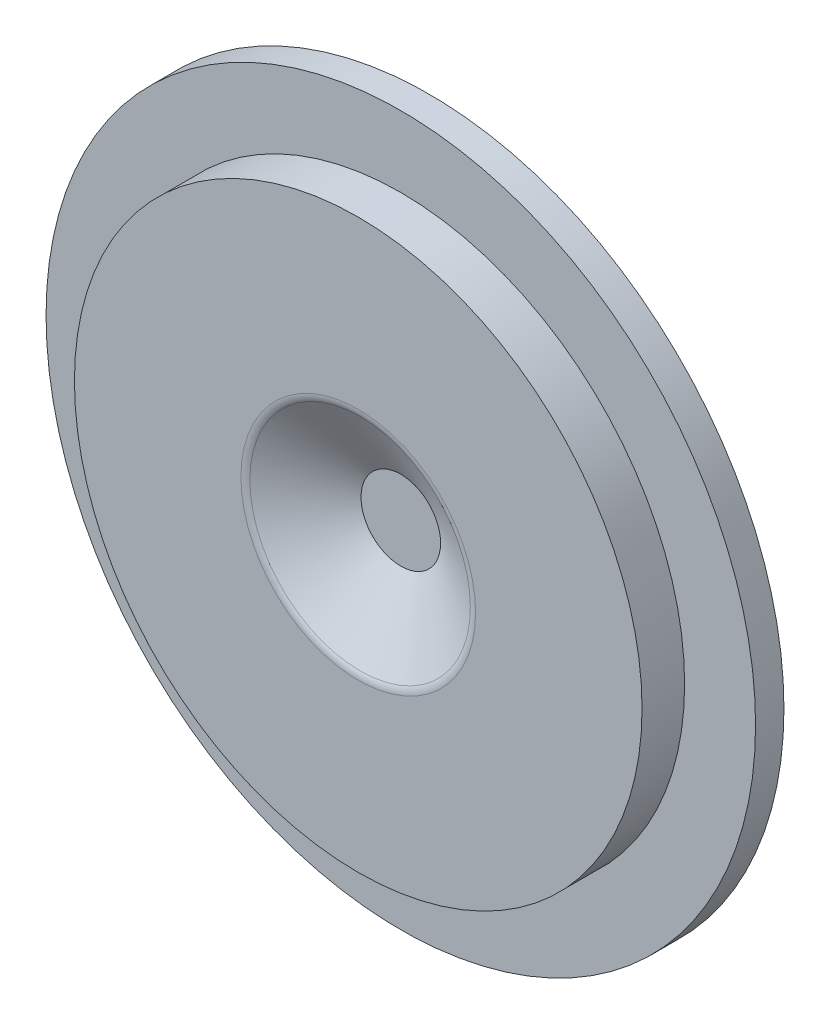
SolidWorks part; units mm, degrees
ref_plane "Front Plane" through (0, 0, 0) normal (0, 0, 1) x (1, 0, 0)
ref_plane "Top Plane" through (0, 0, 0) normal (0, 1, 0) x (1, 0, 0)
ref_plane "Right Plane" through (0, 0, 0) normal (1, 0, 0) x (0, 0, -1)
sketch "Sketch2" plane through (0, 0, 0) normal (0, 0, 1) x (1, 0, 0)
  circle A0 centre (0, 0) radius 100
  dimension "D1" = 200
extrude "Boss-Extrude1" add sketch "Sketch2" along normal blind 25
sketch "Sketch3" plane through (0, 0, 25) normal (0, 0, 1) x (1, 0, 0)
  circle A0 centre (0, 0) radius 40
extrude "Cut-Extrude2" cut sketch "Sketch3" against normal blind 25 draft 60
fillet "Fillet5" radius 5 1 edges at (40, 0, 25)
sketch "Sketch4" plane through (0, 0, 0) normal (0, 0, -1) x (-1, 0, 0)
  circle A0 centre (0, 0) radius 125
  dimension "D1" = 250
extrude "Boss-Extrude2" add sketch "Sketch4" against normal blind 10
